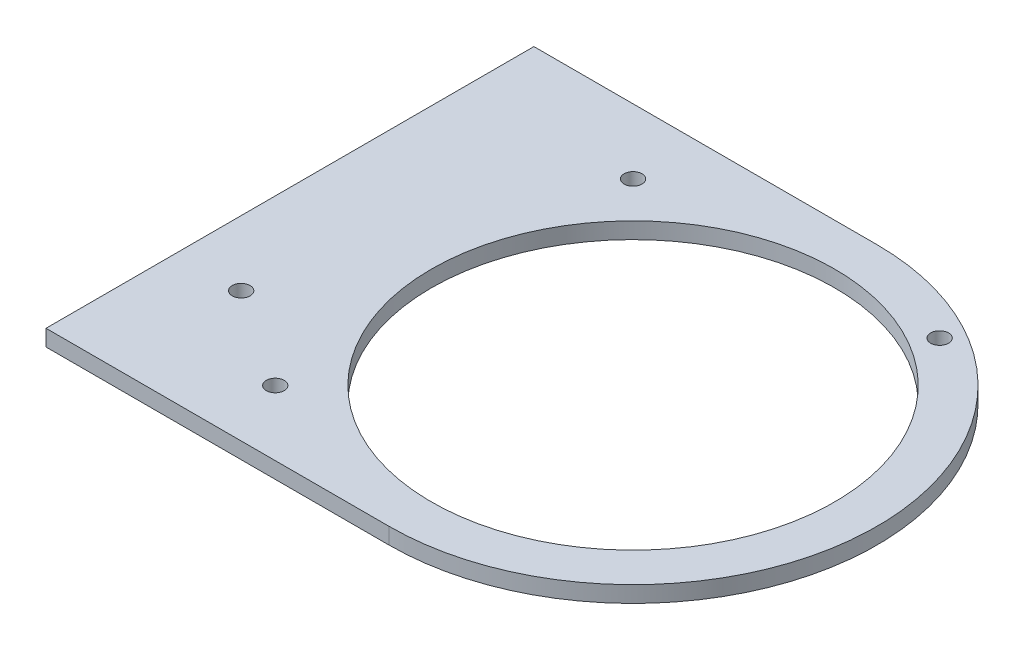
SolidWorks part; units mm, degrees
ref_plane "Front Plane" through (0, 0, 0) normal (0, 0, 1) x (1, 0, 0)
ref_plane "Top Plane" through (0, 0, 0) normal (0, 1, 0) x (1, 0, 0)
ref_plane "Right Plane" through (0, 0, 0) normal (1, 0, 0) x (0, 0, -1)
sketch "Sketch1" plane through (0, 0, 0) normal (0, 0, 1) x (1, 0, 0)
  line L0 (0, 0) -> (40.3547, 419.1) construction
  line L1 (40.3547, 419.1) -> (159.2585, 419.1) construction
  line L2 (159.2585, 419.1) -> (159.2585, 0) construction
  line L3 (159.2585, 0) -> (0, 0) construction
  line L4 (159.2585, -1000) -> (159.2585, 49000) construction
  line L5 (2.0164, 20.9415) -> (40.3547, 419.1) construction
  line L6 (2.0164, 20.9415) -> (41.8323, 17.1077) construction
  line L7 (40.3547, 419.1) -> (80.1706, 415.2662) construction
  line L8 (41.8323, 17.1077) -> (80.1706, 415.2662) construction
  line L9 (64.0085, -1000) -> (64.0085, 49000) construction
  line L10 (-49.0714, 317.5) -> (-124.9206, 324.8034) construction
  line L11 (-26.3513, 414.3375) -> (40.196, 414.3375) construction
  line L12 (-1162.1335, 304.8) -> (48837.8665, 304.8) construction
  line L13 (-126.4915, 292.1) -> (-50.2915, 292.1) construction
  line L14 (-124.9206, 324.8034) -> (-50.2915, 292.1) construction
  line L15 (-49.0714, 317.5) -> (-126.4915, 292.1) construction
  line L16 (40.196, 338.1375) -> (-26.3513, 338.1375) construction
  line L17 (-134.4017, 325.7164) -> (29.8401, 309.9017)
  line L18 (-134.4017, 325.7164) -> (-133.7931, 332.0371)
  line L19 (-133.7931, 332.0371) -> (40.3547, 419.1)
  line L20 (40.3547, 419.1) -> (108.4585, 419.1)
  line L21 (108.4585, 419.1) -> (108.4585, 0) construction
  line L22 (29.8401, 309.9017) -> (0.4102, 4.2603)
  line L23 (0.4102, 4.2603) -> (44.6556, 0)
  line L24 (44.6556, 0) -> (108.4585, 0)
  line L25 (108.4585, 419.1) -> (159.2585, 311.15)
  line L26 (159.2585, 311.15) -> (159.2585, 304.8)
  line L27 (159.2585, 304.8) -> (108.4585, 280.8941)
  line L28 (108.4585, 280.8941) -> (108.4585, 0)
  line L29 (0.4102, 4.2603) -> (1.6331, 16.9603)
  line L30 (0.4102, 4.2603) -> (44.9044, -0.024)
  line L31 (1.6331, 16.9603) -> (46.1273, 12.676)
  line L32 (44.9044, -0.024) -> (46.1273, 12.676)
  arc A0 (-124.9206, 324.8034) -> (-26.3513, 414.3375) centre (-26.3513, 315.3123) cw construction
  arc A1 (73.5335, 304.8) -> (40.196, 338.1375) centre (40.196, 304.8) ccw construction
  arc A2 (149.7335, 304.8) -> (40.196, 414.3375) centre (40.196, 304.8) ccw construction
  arc A3 (-49.0714, 317.5) -> (-26.3513, 338.1375) centre (-26.3513, 315.3123) cw construction
  point P7 (57.6585, 400.05)
  point P10 (45.5182, 6.35)
  point P17 (149.7335, 304.8)
  point P18 (73.5335, 304.8)
  dimension "D9" = 9.525
  dimension "D14" = 25.4
  dimension "D1" = 419.1
  dimension "D2" = 101.6
  dimension "D3" = 19.05
  dimension "D4" = 19.05
  dimension "D5" = 84.5
  dimension "D6" = 40
  dimension "D7" = 400
  dimension "D8" = 95.25
  dimension "D10" = 9.525
  dimension "D11" = 114.3
  dimension "D12" = 76.2
  dimension "D13" = 9.525
  dimension "D15" = 127
  dimension "D16" = 9.525
  dimension "D17" = 209.55
  dimension "D18" = 6.35
  dimension "D19" = 50.8
  dimension "D20" = 44.45
  dimension "D21" = 6.35
  dimension "D22" = 44.7
  dimension "D23" = 12.7
  dimension "D24" = 6.35
sketch "Sketch2" plane through (0, 0, 0) normal (0, 0, 1) x (1, 0, 0)
  line L1 (159.2585, 0) -> (38.3056, 0)
  line L2 (159.2585, 0) -> (159.2585, 3.175)
  line L3 (159.2585, 3.175) -> (38.3056, 3.175)
  line L4 (38.3056, 0) -> (38.3056, 3.175)
  dimension "D1" = 3.175
  dimension "D2" = 6.35
extrude "Boss-Extrude1" add sketch "Sketch2" along normal blind 95.25
sketch "Sketch3" plane through (0, 3.175, 0) normal (0, 1, 0) x (1, 0, 0)
  line L0 (159.2585, -47.625) -> (111.6335, -47.625) construction
  line L1 (159.2585, -95.25) -> (159.2585, 0) construction
  circle A0 centre (111.6335, -47.625) radius 39.37
  dimension "D1" = 78.74
  dimension "D2" = 47.625
extrude "Cut-Extrude2" cut sketch "Sketch3" against normal through all
sketch "Sketch4" plane through (0, 3.175, 0) normal (0, 1, 0) x (1, 0, 0)
  line L0 (159.2585, -95.25) -> (38.3056, -95.25) construction
  line L1 (-201162.1335, 0) -> (248837.8665, 0) construction
  line L2 (111.6335, -95.25) -> (179.0514, -95.25)
  line L3 (179.0514, -95.25) -> (179.0514, 0)
  line L4 (179.0514, 0) -> (111.6335, 0)
  arc A0 (111.6335, -95.25) -> (111.6335, 0) centre (111.6335, -47.625) ccw
extrude "Cut-Extrude3" cut sketch "Sketch4" against normal through all
sketch "Sketch8" plane through (0, 3.175, 0) normal (0, 1, 0) x (1, 0, 0)
  line L1 (146.5585, -82.55) -> (76.7085, -82.55) construction
  line L2 (146.5585, -82.55) -> (146.5585, -12.7) construction
  line L3 (146.5585, -12.7) -> (76.7085, -12.7) construction
  line L4 (76.7085, -82.55) -> (76.7085, -12.7) construction
  line L5 (146.5585, -82.55) -> (76.7085, -12.7) construction
  line L6 (146.5585, -12.7) -> (76.7085, -82.55) construction
  circle A0 centre (76.7085, -12.7) radius 1.75
  circle A1 centre (76.7085, -82.55) radius 1.75
  point P0 (111.6335, -47.625)
  dimension "D2" = 3.5
  dimension "D1" = 69.85
extrude "Cut-Extrude7" cut sketch "Sketch8" against normal through all
sketch "Sketch10" plane through (0, 3.175, 0) normal (0, 1, 0) x (1, 0, 0)
  line L0 (111.6335, -47.625) -> (135.446, -6.3805) construction
  line L2 (38.3056, -95.25) -> (38.3056, 0) construction
  arc A0 (111.6335, -95.25) -> (111.6335, 0) centre (111.6335, -47.625) ccw construction
  circle A1 centre (133.541, -9.6801) radius 1.75
  dimension "D3" = 3.5
  dimension "D1" = 30
  dimension "D2" = 3.81
extrude "Cut-Extrude9" cut sketch "Sketch10" against normal through all
sketch "Sketch11" plane through (0, 3.175, 0) normal (0, 1, 0) x (1, 0, 0)
  line L0 (111.6335, -95.25) -> (38.3056, -95.25) construction
  line L1 (38.3056, 0) -> (44.6556, 0)
  line L2 (38.3056, 0) -> (38.3056, -95.25)
  line L3 (38.3056, -95.25) -> (44.6556, -95.25)
  line L4 (44.6556, 0) -> (44.6556, -95.25)
  dimension "D1" = 6.35
extrude "Cut-Extrude10" cut sketch "Sketch11" against normal through all
sketch "Sketch12" plane through (0, 3.175, 0) normal (0, 1, 0) x (1, 0, 0)
  line L0 (44.6556, -95.25) -> (44.6556, 0) construction
  line L1 (111.6335, -95.25) -> (44.6556, -95.25) construction
  circle A0 centre (57.3556, -69.85) radius 1.75
  circle A1 centre (76.7085, -82.55) radius 1.75 construction
  dimension "D1" = 12.7
  dimension "D2" = 25.4
extrude "Cut-Extrude11" cut sketch "Sketch12" against normal through all
